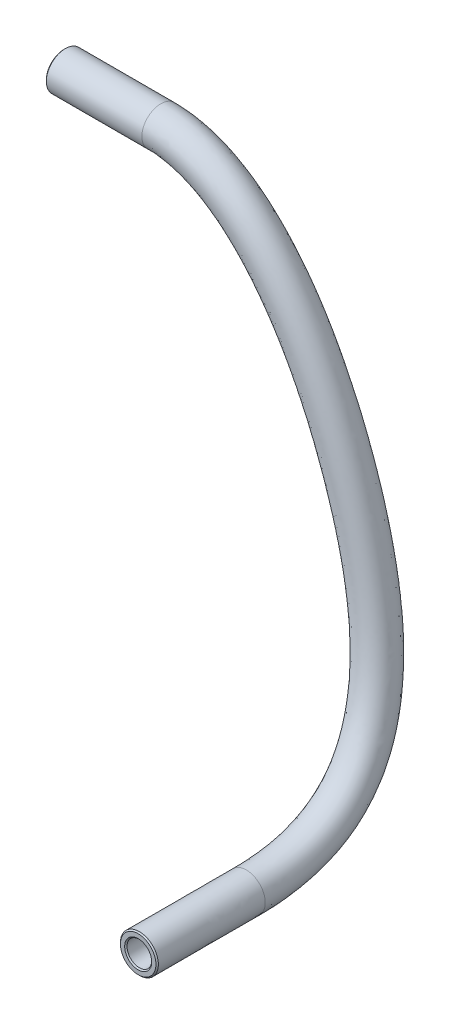
SolidWorks part; units mm, degrees
ref_plane "Front Plane" through (0, 0, 0) normal (0, 0, 1) x (1, 0, 0)
ref_plane "Top Plane" through (0, 0, 0) normal (0, 1, 0) x (1, 0, 0)
ref_plane "Right Plane" through (0, 0, 0) normal (1, 0, 0) x (0, 0, -1)
sketch3d "3DSketch1"
  line L0 (96.825, -106.4823, 33.525) -> (107.025, -106.4823, 33.525)
  line L1 (132.2015, -155.7792, 49.6875) -> (132.2015, -155.7792, 61.0875)
  spline S0 degree 3 poles (107.025, -106.4823, 33.525) (116.3429, -106.4823, 33.525) (130.0473, -131.1307, 32.0984) (132.2015, -155.7792, 34.0685) (132.2015, -155.7792, 49.6875) knots 0 0 0 0 0.484757 1 1 1 1
sketch "Sketch1" plane through (104.925, 0, 0) normal (1, 0, 0) x (0, 0, -1)
  circle A0 centre (-33.525, -106.4823) radius 1.3
  circle A1 centre (-33.525, -106.4823) radius 2
  circle A2 centre (-33.525, -106.4823) radius 3.5 construction
  dimension "D1" = 2.6
  dimension "D2" = 4
sweep "Sweep1" add profiles "Sketch1" path "3DSketch1"
chamfer "Chamfer1" distance 0.127 angle 45 4 edges at (133.8512, -156.9099, 61.0875) (133.2738, -156.5142, 61.0875) (96.825, -104.4823, 33.525) (96.825, -105.1823, 33.525)
